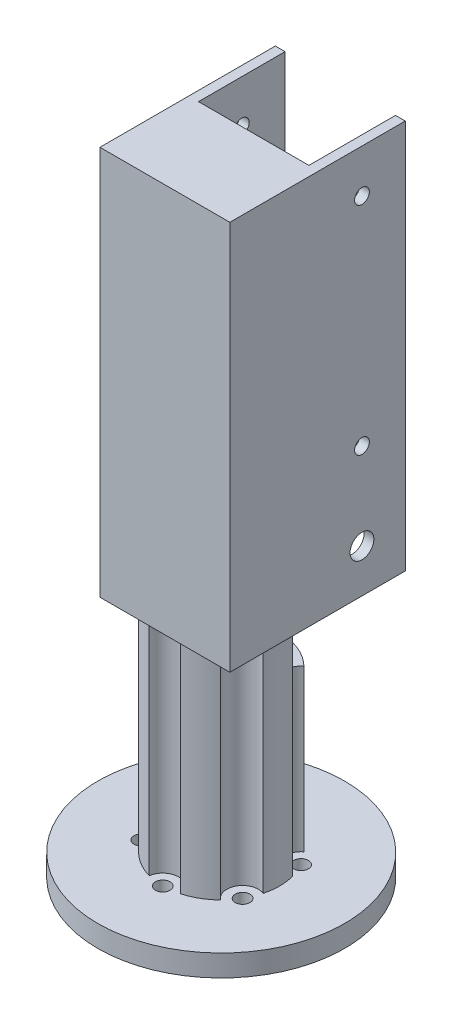
SolidWorks part; units mm, degrees
ref_plane "前视基准面" through (0, 0, 0) normal (0, 0, 1) x (1, 0, 0)
ref_plane "上视基准面" through (0, 0, 0) normal (0, 1, 0) x (1, 0, 0)
ref_plane "右视基准面" through (0, 0, 0) normal (1, 0, 0) x (0, 0, -1)
sketch "草图1" plane through (0, 0, 0) normal (0, 1, 0) x (1, 0, 0)
  circle A0 centre (0, 0) radius 13.5 construction
  circle A1 centre (0, 0) radius 28.5
  circle A2 centre (0, 13.5) radius 1.7
  circle A3 centre (11.6913, 6.75) radius 1.7
  circle A4 centre (11.6913, -6.75) radius 1.7
  circle A5 centre (0, -13.5) radius 1.7
  circle A6 centre (-11.6913, -6.75) radius 1.7
  circle A7 centre (-11.6913, 6.75) radius 1.7
  point P18 (0, 0)
  dimension "D1" = 27
  dimension "D2" = 57
  dimension "D3" = 3.4
  dimension "D4" = 6
extrude "凸台-拉伸1" add sketch "草图1" along normal blind 5
sketch "草图2" plane through (0, 5, 0) normal (0, 1, 0) x (1, 0, 0)
  circle A0 centre (0, 0) radius 13.5
  dimension "D1" = 27
extrude "凸台-拉伸2" add sketch "草图2" along normal blind 50
sketch "草图3" plane through (0, 5, 0) normal (0, -1, 0) x (1, 0, 0)
  circle A0 centre (-11.6913, -6.75) radius 3.65
  arc A1 (-12.447, -5.2272) -> (-10.7503, -8.1658) centre (0, 0) ccw construction
  circle A2 centre (-11.6913, 6.75) radius 3.65
  circle A3 centre (0, 13.5) radius 3.65
  circle A4 centre (11.6913, 6.75) radius 3.65
  circle A5 centre (11.6913, -6.75) radius 3.65
  circle A6 centre (0, -13.5) radius 3.65
  point P18 (0, 0)
  dimension "D1" = 7.3
  dimension "D2" = 6
extrude "切除-拉伸1" cut sketch "草图3" against normal blind 50
sketch "草图4" plane through (0, 55, 0) normal (0, 1, 0) x (1, 0, 0)
  line L1 (-15, -27.5) -> (15, -27.5)
  line L2 (-15, -27.5) -> (-15, 27.5)
  line L3 (-15, 27.5) -> (15, 27.5)
  line L4 (15, -27.5) -> (15, 27.5)
  line L5 (-15, -27.5) -> (15, 27.5) construction
  line L6 (-15, 27.5) -> (15, -27.5) construction
  point P0 (0, 0)
  dimension "D1" = 55
  dimension "D2" = 30
extrude "凸台-拉伸3" add sketch "草图4" along normal blind 90
sketch "草图6" plane through (15, 0, 0) normal (1, 0, 0) x (0, 0, -1)
  line L0 (28.5, 5) -> (-28.5, 5) construction
  line L1 (27.5, 145) -> (27.5, 55) construction
  circle A0 centre (17.5, 85) radius 1.7
  circle A1 centre (17.5, 135) radius 1.7
  circle A2 centre (17.5, 65) radius 2.75
  dimension "D1" = 80
  dimension "D2" = 10
  dimension "D3" = 3.4
  dimension "D4" = 3.4
  dimension "D5" = 50
  dimension "D6" = 5.5
  dimension "D7" = 20
extrude "切除-拉伸2" cut sketch "草图6" against normal blind 50
sketch "草图7" plane through (0, 0, -27.5) normal (0, 0, -1) x (-1, 0, 0)
  line L0 (0, -7.2242) -> (0, 177.2852) construction
  line L2 (12.75, 152.9873) -> (-12.75, 152.9873)
  line L3 (12.75, 152.9873) -> (12.75, 42.1438)
  line L4 (12.75, 42.1438) -> (-12.75, 42.1438)
  line L5 (-12.75, 152.9873) -> (-12.75, 42.1438)
  line L6 (12.75, 152.9873) -> (-12.75, 42.1438) construction
  line L7 (12.75, 42.1438) -> (-12.75, 152.9873) construction
  point P3 (0, 97.5655)
  dimension "D1" = 25.5
extrude "切除-拉伸3" cut sketch "草图7" against normal blind 20
sketch "草图8" plane through (0, 55, 0) normal (0, -1, 0) x (1, 0, 0)
  line L1 (16.9162, 13.0066) -> (-19.7934, 13.0066)
  line L2 (16.9162, 13.0066) -> (16.9162, 31.6614)
  line L3 (16.9162, 31.6614) -> (-19.7934, 31.6614)
  line L4 (-19.7934, 13.0066) -> (-19.7934, 31.6614)
extrude "切除-拉伸4" cut sketch "草图8" against normal blind 110
